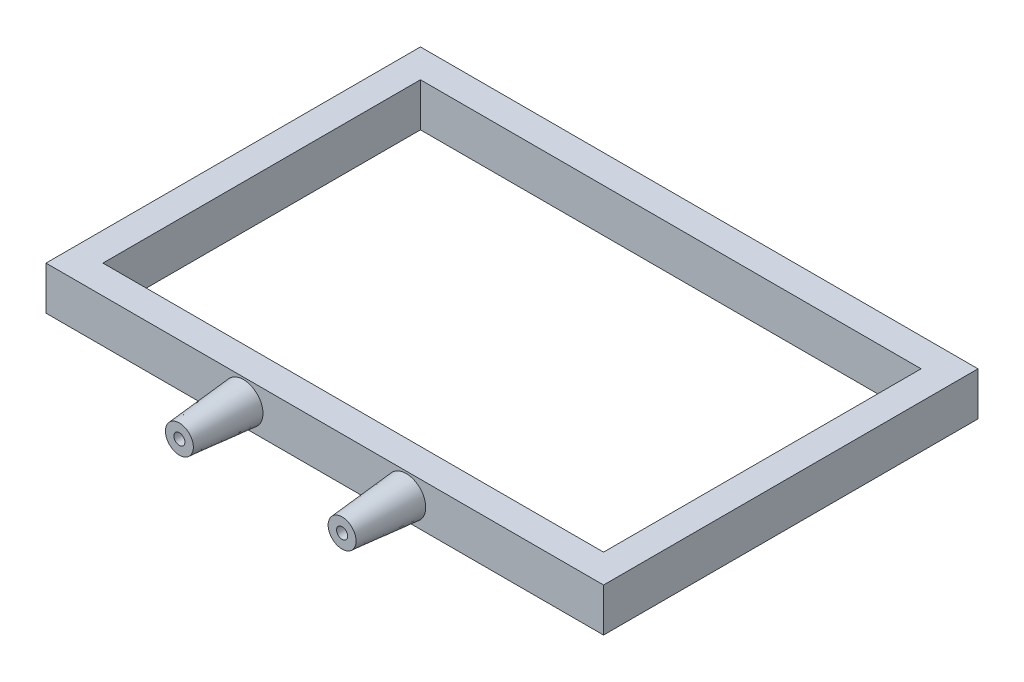
SolidWorks part; units mm, degrees
ref_plane "正面" through (0, 0, 0) normal (0, 0, 1) x (1, 0, 0)
ref_plane "平面" through (0, 0, 0) normal (0, 1, 0) x (1, 0, 0)
ref_plane "右側面" through (0, 0, 0) normal (1, 0, 0) x (0, 0, -1)
sketch "ｽｹｯﾁ1" plane through (0, 0, 0) normal (0, 1, 0) x (1, 0, 0)
  line L1 (-78.375, 52.636) -> (78.375, 52.636)
  line L2 (-78.375, 52.636) -> (-78.375, -52.636)
  line L3 (-78.375, -52.636) -> (78.375, -52.636)
  line L4 (78.375, 52.636) -> (78.375, -52.636)
  line L5 (-78.375, 52.636) -> (78.375, -52.636) construction
  line L6 (-78.375, -52.636) -> (78.375, 52.636) construction
  point P0 (0, 0)
  dimension "D1" = 156.75
  dimension "D2" = 105.272
extrude "ﾎﾞｽ - 押し出し1" add sketch "ｽｹｯﾁ1" along normal blind 12.2
ref_plane "平面1" through (0, 12.2, 0) normal (0, 1, 0) x (1, 0, 0)
sketch "ｽｹｯﾁ2" plane through (0, 12.2, 0) normal (0, 1, 0) x (1, 0, 0)
  line L1 (44.016, 0) -> (36.3764, 0)
  line L2 (44.016, 13.8901) -> (36.3764, 13.8901)
  line L3 (-44.016, 13.8901) -> (-36.3764, 13.8901)
  line L4 (-44.016, 13.8901) -> (-44.016, 0)
  line L5 (-44.016, 0) -> (-36.3764, 0)
  line L6 (-36.3764, 13.8901) -> (-36.3764, 0)
  line L7 (-44.016, 13.8901) -> (-36.3764, 0) construction
  line L8 (-44.016, 0) -> (-36.3764, 13.8901) construction
  line L9 (0, 52.636) -> (0, -52.636) construction
  line L10 (78.375, 52.636) -> (-78.375, 52.636) construction
  line L11 (-78.375, -52.636) -> (78.375, -52.636) construction
  line L12 (44.016, 13.8901) -> (44.016, 0)
  line L13 (36.3764, 13.8901) -> (36.3764, 0)
  arc A0 (-44.016, 13.8901) -> (-36.3764, 13.8901) centre (-40.1962, 12.4004) cw
  arc A1 (-44.016, 0) -> (-36.3764, 0) centre (-40.1962, 1.4897) ccw
  arc A2 (44.016, 0) -> (36.3764, 0) centre (40.1962, 1.4897) cw
  arc A3 (44.016, 13.8901) -> (36.3764, 13.8901) centre (40.1962, 12.4004) ccw
  point P0 (-40.1962, 6.9451)
  dimension "D3" = 52.636
extrude "ｶｯﾄ - 押し出し1" cut sketch "ｽｹｯﾁ2" against normal blind 6.1 contours A0 L3 | L6 L3 L4 L5 | L5 A1 | L2 A3 | L2 L13 L1 L12 | A2 L1
ref_plane "平面2" through (0, 0, 52.636) normal (0, 0, 1) x (1, 0, 0)
sketch "ｽｹｯﾁ4" plane through (0, 0, 52.636) normal (0, 0, 1) x (1, 0, 0)
  line L0 (0, 12.2) -> (0, 0) construction
  line L1 (-78.375, 12.2) -> (78.375, 12.2) construction
  line L2 (-78.375, 0) -> (78.375, 0) construction
  line L3 (-78.375, 12.2) -> (-78.375, 0) construction
  circle A0 centre (-22.875, 6.1) radius 5.5
  circle A2 centre (22.875, 6.1) radius 5.5
  dimension "D1" = 6.1
  dimension "D3" = 11
  dimension "D2" = 55.5
extrude "ﾎﾞｽ - 押し出し2" add sketch "ｽｹｯﾁ4" along normal blind 18 draft 5 contours A0 | A2
sketch "ｽｹｯﾁ6" plane through (0, 0, 52.636) normal (0, 0, 1) x (1, 0, 0)
  line L0 (0, 12.2) -> (0, 0) construction
  line L1 (-78.375, 12.2) -> (78.375, 12.2) construction
  line L2 (-78.375, 0) -> (78.375, 0) construction
  circle A0 centre (-22.875, 6.1) radius 1.55
  circle A1 centre (22.875, 6.1) radius 1.55
  dimension "D1" = 3.1
extrude "ｶｯﾄ - 押し出し2" cut sketch "ｽｹｯﾁ6" along normal up to next
sketch "ｽｹｯﾁ7" plane through (0, 0, 0) normal (0, 1, 0) x (1, 0, 0)
  line L0 (0, -52.636) -> (0, -72.6331) construction
  line L1 (-26.375, -60.636) -> (-19.375, -60.636)
  line L2 (-26.375, -60.636) -> (-26.375, -57.136)
  line L3 (-26.375, -57.136) -> (-19.375, -57.136)
  line L4 (-19.375, -60.636) -> (-19.375, -57.136)
  line L5 (-6.71, -52.636) -> (6.71, -52.636) construction
  line L6 (-26.8002, -70.636) -> (-18.9498, -70.636) construction
  line L7 (-26.8002, -70.636) -> (-26.375, -60.636) construction
  line L8 (-18.9498, -70.636) -> (-19.375, -60.636) construction
  line L9 (19.375, -60.636) -> (19.375, -57.136)
  line L10 (26.375, -57.136) -> (19.375, -57.136)
  line L11 (26.375, -60.636) -> (26.375, -57.136)
  line L12 (26.375, -60.636) -> (19.375, -60.636)
  dimension "D1" = 7
  dimension "D2" = 3.5
  dimension "D3" = 10
extrude "ｶｯﾄ - 押し出し3" cut sketch "ｽｹｯﾁ7" along normal blind 9.1
ref_plane "平面3" through (0, 0, 0) normal (0, -1, 0) x (-1, 0, 0)
sketch "ｽｹｯﾁ8" plane through (0, 0, 0) normal (0, -1, 0) x (-1, 0, 0)
  line L0 (78.375, 52.636) -> (78.375, -52.636) construction
  line L1 (-70.375, 44.636) -> (70.375, 44.636)
  line L2 (-70.375, 44.636) -> (-70.375, -44.636)
  line L3 (-70.375, -44.636) -> (70.375, -44.636)
  line L4 (70.375, 44.636) -> (70.375, -44.636)
  line L5 (-70.375, 44.636) -> (70.375, -44.636) construction
  line L6 (-70.375, -44.636) -> (70.375, 44.636) construction
  line L7 (-78.375, 52.636) -> (78.375, 52.636) construction
  point P0 (0, 0)
  point P8 (78.375, 0)
  dimension "D1" = 8
  dimension "D2" = 8
extrude "ｶｯﾄ - 押し出し4" cut sketch "ｽｹｯﾁ8" against normal through all
